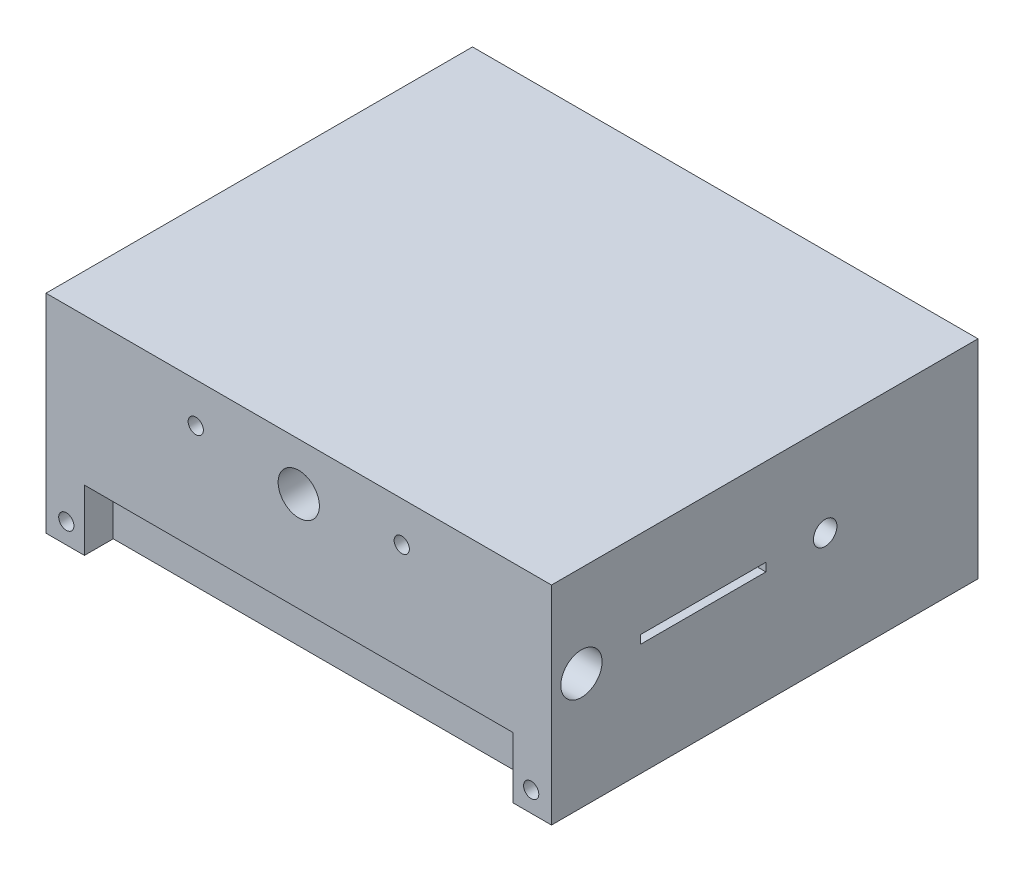
SolidWorks part; units mm, degrees
ref_plane "Front Plane" through (0, 0, 0) normal (0, 0, 1) x (1, 0, 0)
ref_plane "Top Plane" through (0, 0, 0) normal (0, 1, 0) x (1, 0, 0)
ref_plane "Right Plane" through (0, 0, 0) normal (1, 0, 0) x (0, 0, -1)
sketch "Sketch1" plane through (0, 0, 0) normal (1, 0, 0) x (0, 0, -1)
  line L1 (-133.35, -65.0034) -> (133.35, -65.0034)
  line L2 (-133.35, -65.0034) -> (-133.35, 65.0034)
  line L3 (-133.35, 65.0034) -> (133.35, 65.0034)
  line L4 (133.35, -65.0034) -> (133.35, 65.0034)
  line L5 (-133.35, -65.0034) -> (133.35, 65.0034) construction
  line L6 (-133.35, 65.0034) -> (133.35, -65.0034) construction
  point P0 (0, 0)
  dimension "D1" = 130.0069
  dimension "D2" = 266.7
extrude "Boss-Extrude1" add sketch "Sketch1" along normal blind 316.0929
sketch "Sketch2" plane through (0, 0, 133.35) normal (0, 0, 1) x (1, 0, 0)
  line L0 (316.0929, 65.0034) -> (0, 65.0034) construction
  line L1 (0, 65.0034) -> (0, -65.0034) construction
  line L2 (158.0465, 65.0034) -> (158.0465, 35.219) construction
  circle A0 centre (93.6394, 39.9903) radius 4.7625
  circle A1 centre (222.4535, 39.9903) radius 4.7625
  circle A2 centre (303.3929, -52.3034) radius 4.7625
  circle A3 centre (12.7, -52.3034) radius 4.7625
  circle A4 centre (158.0465, 35.219) radius 12.8984
  point P15 (158.0465, 31.851)
  dimension "D1" = 9.525
  dimension "D9" = 25.7969
  dimension "D2" = 128.814
  dimension "D3" = 25.0131
  dimension "D4" = 80.9394
  dimension "D5" = 92.2937
  dimension "D6" = 80.9394
  dimension "D7" = 92.2937
  dimension "D8" = 12.7
  dimension "D10" = 29.7845
extrude "Cut-Extrude1" cut sketch "Sketch2" against normal blind 266.7
sketch "Sketch3" plane through (316.0929, 0, 0) normal (1, 0, 0) x (0, 0, -1)
  line L0 (-133.35, 65.0034) -> (-133.35, -65.0034) construction
  line L1 (133.35, 65.0034) -> (-133.35, 65.0034) construction
  line L3 (-77.5613, 5.0444) -> (0.7263, 5.0444)
  line L4 (-77.5613, 5.0444) -> (-77.5613, 10.3069)
  line L5 (-77.5613, 10.3069) -> (0.7263, 10.3069)
  line L6 (0.7263, 5.0444) -> (0.7263, 10.3069)
  line L7 (-77.5613, 5.0444) -> (0.7263, 10.3069) construction
  line L8 (-77.5613, 10.3069) -> (0.7263, 5.0444) construction
  circle A0 centre (-114.6175, 7.6756) radius 12.8984
  circle A1 centre (37.7825, 7.6756) radius 7.3422
  point P8 (-38.4175, 7.6756)
  point P13 (-38.4175, 5.0444)
  point P14 (0, 0)
  point P15 (37.7825, 7.6756)
  dimension "D2" = 152.4
  dimension "D3" = 25.7969
  dimension "D5" = 14.6844
  dimension "D1" = 18.7325
  dimension "D4" = 57.3278
  dimension "D6" = 37.0562
  dimension "D7" = 5.2625
  dimension "D8" = 78.2875
extrude "Cut-Extrude2" cut sketch "Sketch3" against normal blind 332.74
sketch "Sketch4" plane through (0, 0, 133.35) normal (0, 0, 1) x (1, 0, 0)
  line L0 (316.0929, -65.0034) -> (0, -65.0034) construction
  line L1 (24.0496, -65.0034) -> (292.0433, -65.0034)
  line L2 (24.0496, -65.0034) -> (24.0496, -26.9034)
  line L3 (24.0496, -26.9034) -> (292.0433, -26.9034)
  line L4 (292.0433, -65.0034) -> (292.0433, -26.9034)
  circle A0 centre (12.7, -52.3034) radius 4.7625 construction
  circle A1 centre (303.3929, -52.3034) radius 4.7625 construction
  dimension "D1" = 11.3496
  dimension "D2" = 11.3496
  dimension "D3" = 38.1
extrude "Cut-Extrude3" cut sketch "Sketch4" against normal blind 18
ref_plane "Plane1" through (0, 0, 0) normal (0, 0, 1) x (1, 0, 0)
mirror "Mirror1" about plane through (0, 0, 0) normal (0, 0, 1) of "Cut-Extrude3"
